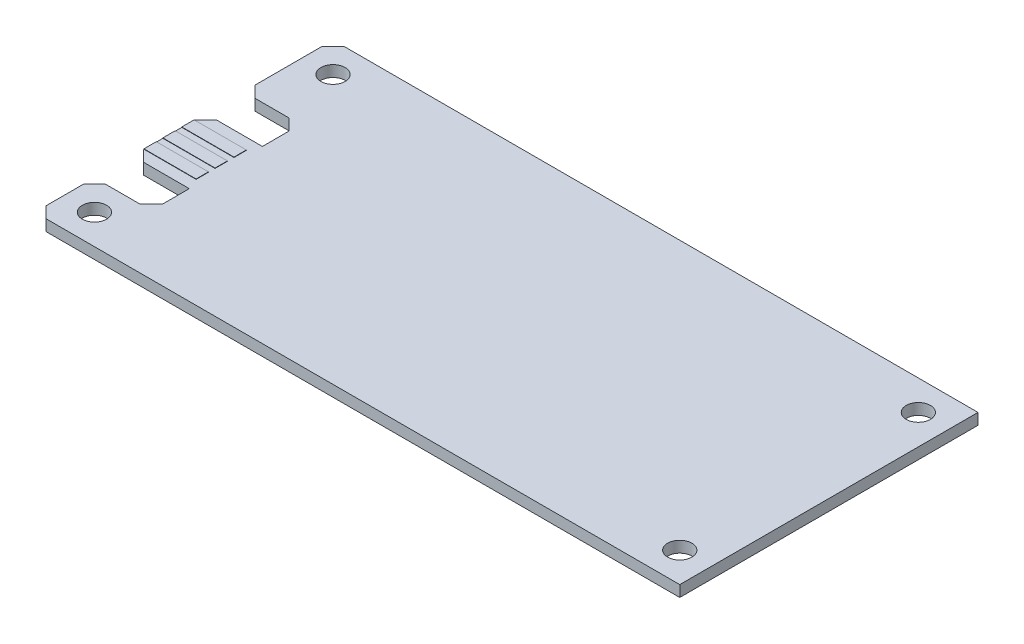
SolidWorks part; units mm, degrees
ref_plane "Front Plane" through (0, 0, 0) normal (0, 0, 1) x (1, 0, 0)
ref_plane "Top Plane" through (0, 0, 0) normal (0, 1, 0) x (1, 0, 0)
ref_plane "Right Plane" through (0, 0, 0) normal (1, 0, 0) x (0, 0, -1)
sketch "Sketch1" plane through (0, 0, 0) normal (0, 1, 0) x (1, 0, 0)
  line L0 (0, 0) -> (45, 0) construction
  line L1 (-41.5, 20) -> (45, 20)
  line L2 (-41.5, 20) -> (-41.5, -20)
  line L3 (-41.5, -20) -> (45, -20)
  line L4 (45, 20) -> (45, -20)
  dimension "D1" = 20
  dimension "D2" = 41.5
  dimension "D3" = 45
  dimension "D4" = 20
extrude "Boss-Extrude1" add sketch "Sketch1" along normal blind 1.5
sketch "Sketch2" plane through (0, 1.5, 0) normal (0, 1, 0) x (1, 0, 0)
  line L0 (-41.5, 20) -> (-41.5, -20) construction
  line L1 (-41.5, 8) -> (-33.88, 8)
  line L2 (-41.5, 8) -> (-41.5, 2.9022)
  line L3 (-41.5, 2.9022) -> (-33.88, 2.9022)
  line L4 (-33.88, 8) -> (-33.88, 2.9022)
  line L5 (-41.5, -6.9022) -> (-41.5, 2.9022) construction
  line L6 (-41.5, -6.9022) -> (-33.88, -6.9022)
  line L7 (-41.5, -6.9022) -> (-41.5, -12)
  line L8 (-41.5, -12) -> (-33.88, -12)
  line L9 (-33.88, -6.9022) -> (-33.88, -12)
  line L10 (-41.5, -2) -> (-15.4253, -2) construction
  dimension "D1" = 9.8044
  dimension "D2" = 20
  dimension "D3" = 2
  dimension "D4" = 7.62
extrude "Cut-Extrude1" cut sketch "Sketch2" against normal through all
chamfer "Chamfer2" distance 1.5 angle 45 8 edges at (-41.5, 0.75, 6.9022) (-41.5, 0.75, -2.9022) (-41.5, 0.75, -8) (-41.5, 0.75, 12) (-41.5, 0.75, -20) (-41.5, 0.75, 20) (-33.88, 0.75, -8) (-33.88, 0.75, 12)
sketch "Sketch4" plane through (0, 0, 0) normal (0, -1, 0) x (1, 0, 0)
  line L1 (-37.5, -16) -> (41, -16) construction
  line L2 (-37.5, -16) -> (-37.5, 16) construction
  line L3 (-37.5, 16) -> (41, 16) construction
  line L4 (41, -16) -> (41, 16) construction
  circle A0 centre (-37.5, 16) radius 1.625
  circle A1 centre (41, 16) radius 1.625
  circle A2 centre (41, -16) radius 1.625
  circle A3 centre (-37.5, -16) radius 1.625
  circle A4 centre (-37.5, -16) radius 3.175 construction
  dimension "D1" = 3.25
  dimension "D2" = 6.35
  dimension "D3" = 16
  dimension "D4" = 16
  dimension "D5" = 37.5
  dimension "D6" = 41
extrude "Cut-Extrude2" cut sketch "Sketch4" against normal through all
sketch "Sketch5" plane through (0, 1.5, 0) normal (0, 1, 0) x (1, 0, 0)
  line L0 (-18, -8) -> (-18, 10.6)
  line L1 (-18, 10.6) -> (-15.4, 10.6)
  line L2 (-15.4, 10.6) -> (-8, 18)
  line L3 (-8, 18) -> (10.6, 18)
  line L4 (10.6, 18) -> (10.6, 15.4)
  line L5 (10.6, 15.4) -> (15.75, 10.25)
  line L6 (15.75, 10.25) -> (18, 10.25)
  line L7 (18, 10.25) -> (18, -10.25)
  line L8 (18, -10.25) -> (15.75, -10.25)
  line L9 (15.75, -10.25) -> (8, -18)
  line L10 (8, -18) -> (-12, -18)
  line L11 (-12, -18) -> (-12, -14)
  line L12 (-12, -14) -> (-18, -8)
  line L13 (0, 0) -> (0, 18) construction
  line L14 (0, 0) -> (0, -18) construction
  line L15 (0, 0) -> (18, 0) construction
  line L16 (0, 0) -> (-18, 0) construction
  dimension "D1" = 10.6
  dimension "D2" = 2.6
  dimension "D3" = 18
  dimension "D4" = 10.25
  dimension "D5" = 2.6
  dimension "D6" = 45
  dimension "D7" = 12
  dimension "D8" = 4
  dimension "D9" = 2.25
sketch "Sketch3" plane through (0, 1.5, 0) normal (0, 1, 0) x (1, 0, 0)
  line L0 (-41.5, 2.9022) -> (-41.5, -6.9022) construction
  line L1 (-41.5, 1.3655) -> (-34.5, 1.3655)
  line L2 (-41.5, 1.3655) -> (-41.5, -0.2855)
  line L3 (-41.5, -0.2855) -> (-34.5, -0.2855)
  line L4 (-34.5, 1.3655) -> (-34.5, -0.2855)
  line L5 (-34.5, -3.7145) -> (-34.5, -2.8255) construction
  line L6 (-41.5, -1.1745) -> (-34.5, -1.1745)
  line L7 (-41.5, -1.1745) -> (-41.5, -2.8255)
  line L8 (-41.5, -2.8255) -> (-34.5, -2.8255)
  line L9 (-34.5, -1.1745) -> (-34.5, -2.8255)
  line L10 (-41.5, -3.7145) -> (-34.5, -3.7145)
  line L11 (-41.5, -3.7145) -> (-41.5, -5.3655)
  line L12 (-41.5, -5.3655) -> (-34.5, -5.3655)
  line L13 (-34.5, -3.7145) -> (-34.5, -5.3655)
  line L14 (-34.5, -1.1745) -> (-34.5, -0.2855) construction
  line L15 (-34.5, 1.3655) -> (-34.5, 2.9022) construction
  line L16 (-40, 2.9022) -> (-33.88, 2.9022) construction
  line L17 (-34.5, -5.3655) -> (-34.5, -6.9022) construction
  line L18 (-33.88, -6.9022) -> (-40, -6.9022) construction
  dimension "D1" = 2.54
  dimension "D2" = 7
  dimension "D3" = 1.651
extrude "Boss-Extrude2" add sketch "Sketch3" along normal blind 0.05 and the other way offset from surface (1.55 mm away) 0.05 other way up to face at (-37.5, 0, -17.625)
